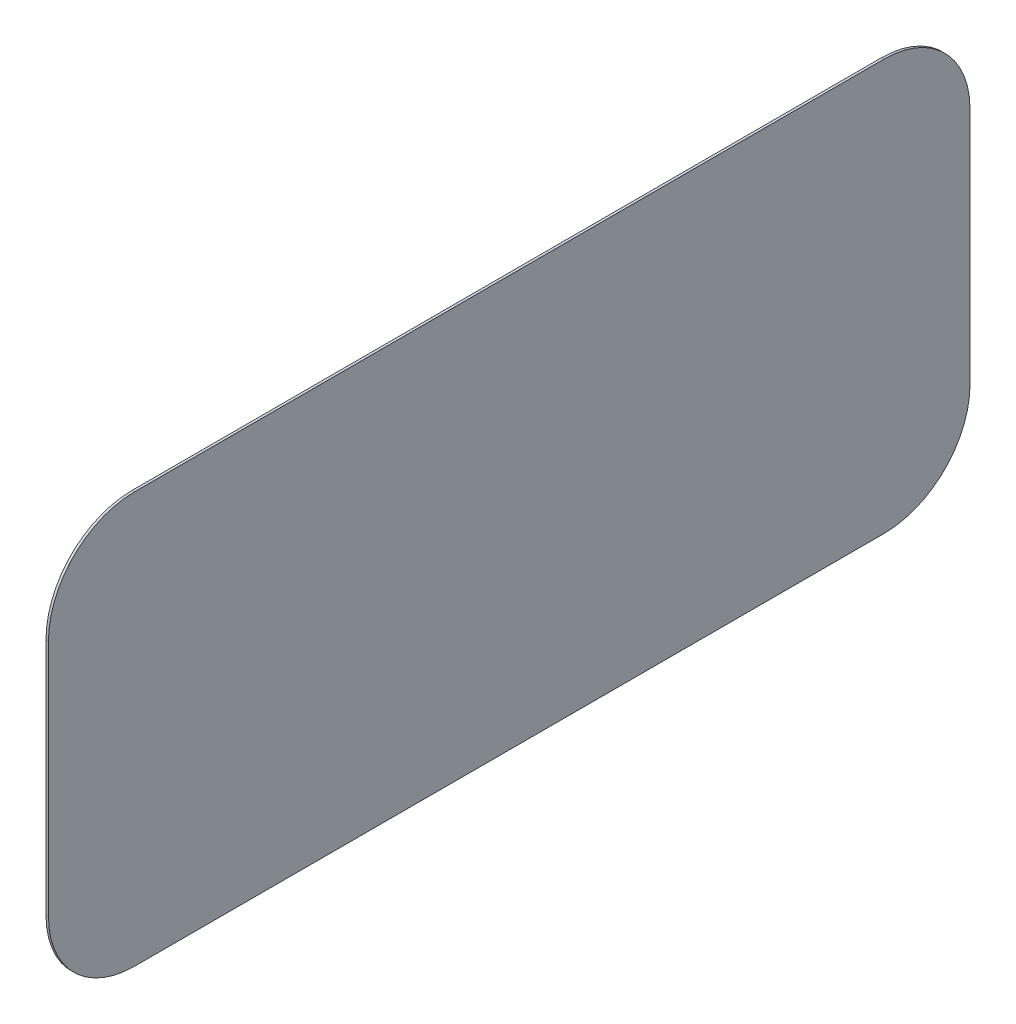
SolidWorks part; units mm, degrees
ref_plane "Front Plane" through (0, 0, 0) normal (0, 0, 1) x (1, 0, 0)
ref_plane "Top Plane" through (0, 0, 0) normal (0, 1, 0) x (1, 0, 0)
ref_plane "Right Plane" through (0, 0, 0) normal (1, 0, 0) x (0, 0, -1)
sketch "Sketch1" plane through (0, 0, 0) normal (1, 0, 0) x (0, 0, -1)
sketch "Sketch2" plane through (0, 0, 0) normal (1, 0, 0) x (0, 0, -1)
  line L0 (0, 0) -> (3050, 0)
  line L1 (3400, 350) -> (3400, 1322)
  line L2 (3050, 1672) -> (0, 1672)
  line L3 (-350, 1322) -> (-350, 350)
  arc A0 (3050, 0) -> (3400, 350) centre (3050, 350) ccw
  arc A1 (3400, 1322) -> (3050, 1672) centre (3050, 1322) ccw
  arc A2 (0, 1672) -> (-350, 1322) centre (0, 1322) ccw
  arc A3 (-350, 350) -> (0, 0) centre (0, 350) ccw
  dimension "D2" = 972
  dimension "D3" = 350
  dimension "D1" = 3050
extrude "Boss-Extrude1" add sketch "Sketch2" against normal blind 10
